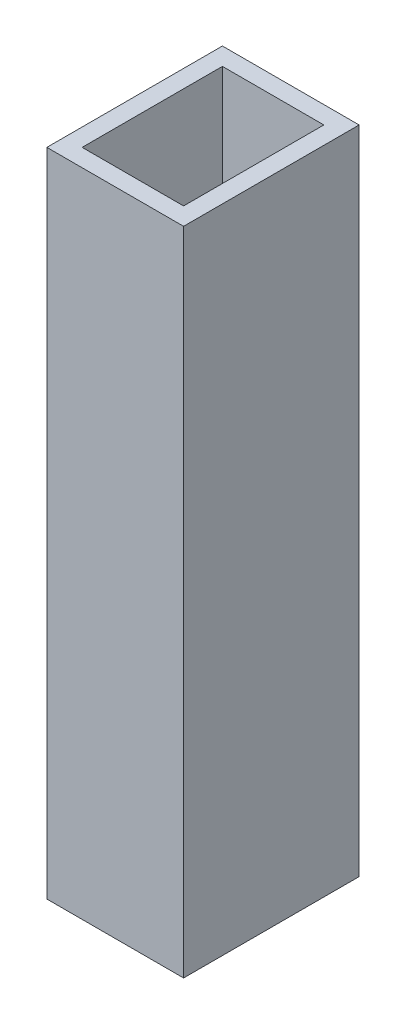
SolidWorks part; units mm, degrees
ref_plane "Front Plane" through (0, 0, 0) normal (0, 0, 1) x (1, 0, 0)
ref_plane "Top Plane" through (0, 0, 0) normal (0, 1, 0) x (1, 0, 0)
ref_plane "Right Plane" through (0, 0, 0) normal (1, 0, 0) x (0, 0, -1)
sketch "Sketch2" plane through (-0.0001, -112.6002, -0.0009) normal (0, -1, 0) x (1, 0, 0)
  line L13 (266.323, -12.06) -> (250.8206, -12.06)
  line L181 (266.323, -12.06) -> (250.8206, -12.06)
  line L230 (250.8206, -12.06) -> (250.8206, -31.965)
  line L231 (250.8206, -12.06) -> (250.8206, -31.965)
  line L232 (250.8206, -31.965) -> (266.323, -31.965)
  line L233 (250.8206, -31.965) -> (266.323, -31.965)
  line L234 (266.323, -31.965) -> (266.323, -12.06)
  line L235 (266.323, -31.965) -> (266.323, -12.06)
  dimension "D1" = 0
extrude "Boss-Extrude1" add sketch "Sketch2" along normal up to surface (73.81 mm away)
shell "Shell1" thickness 2
equation "\"tubewidth\"= 3"
